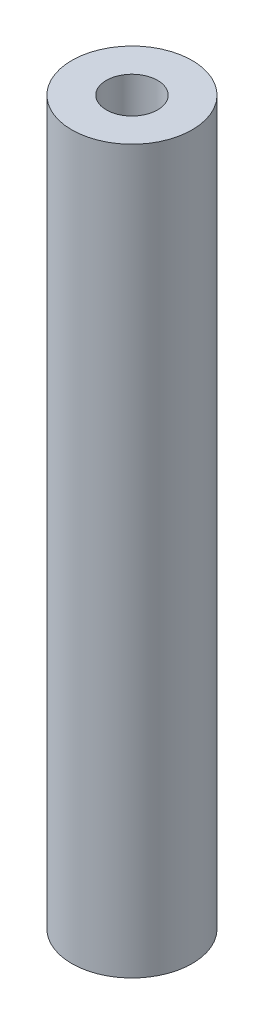
SolidWorks part; units mm, degrees
ref_plane "Front Plane" through (0, 0, 0) normal (0, 0, 1) x (1, 0, 0)
ref_plane "Top Plane" through (0, 0, 0) normal (0, 1, 0) x (1, 0, 0)
ref_plane "Right Plane" through (0, 0, 0) normal (1, 0, 0) x (0, 0, -1)
sketch "Sketch1" plane through (0, 0, 0) normal (0, 1, 0) x (1, 0, 0)
  circle A0 centre (0, 0) radius 3.175
  dimension "D1" = 6.35
extrude "Boss-Extrude1" add sketch "Sketch1" along normal blind 38.1
hole_wizard "Tap Drill for #6-32 Tap1" positions "Sketch3" profile "Sketch2" hole size "#6-32" standard "ANSI Inch" end condition through all
sketch "Sketch3" plane through (0, 38.1, 0) normal (0, 1, 0) x (1, 0, 0)
  point P0 (0, 0)
sketch "Sketch2" plane through (0, 38.1, 0) normal (1, 0, 0) x (0, 0, 1)
  line L0 (0, 0) -> (0, 38.1)
  line L1 (0, 38.1) -> (1.3525, 38.1)
  line L2 (1.3525, 38.1) -> (1.3525, 0)
  line L5 (1.3525, 0) -> (0, 0)
  line L11 (0, -6.35) -> (0, 107.95) construction
  dimension "Thru Hole Dia." = 2.7051
  dimension "Thru Hole Depth" = 38.1
